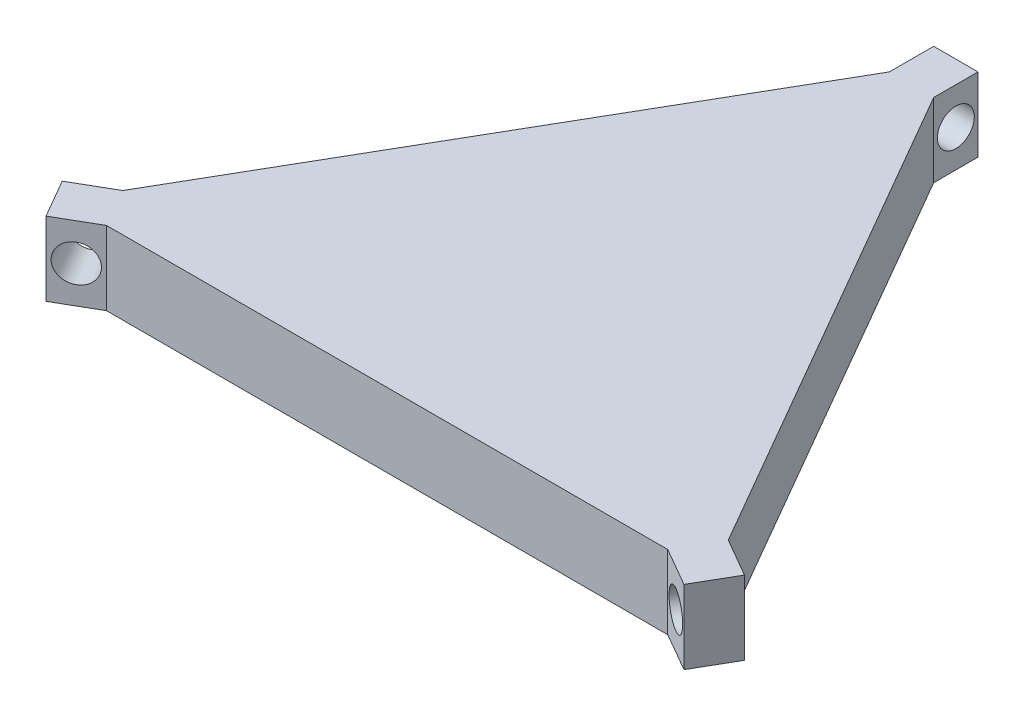
SolidWorks part; units mm, degrees
ref_plane "Front Plane" through (0, 0, 0) normal (0, 0, 1) x (1, 0, 0)
ref_plane "Top Plane" through (0, 0, 0) normal (0, 1, 0) x (1, 0, 0)
ref_plane "Right Plane" through (0, 0, 0) normal (1, 0, 0) x (0, 0, -1)
sketch "Sketch1" plane through (0, 0, 0) normal (0, 1, 0) x (1, 0, 0)
  line L6 (-3, 71.0141) -> (-41, 5.1962)
  line L7 (3, 71.0141) -> (41, 5.1962)
  line L8 (-38, 0) -> (38, 0)
  line L10 (-41, 5.1962) -> (-46.1962, 2.1962)
  line L11 (-38, 0) -> (-43.1962, -3)
  line L12 (-46.1962, 2.1962) -> (-43.1962, -3)
  line L14 (38, 0) -> (43.1962, -3)
  line L15 (41, 5.1962) -> (46.1962, 2.1962)
  line L16 (43.1962, -3) -> (46.1962, 2.1962)
  line L18 (3, 71.0141) -> (3, 77.0141)
  line L19 (-3, 71.0141) -> (-3, 77.0141)
  line L20 (3, 77.0141) -> (-3, 77.0141)
  point P1 (0, 0)
  dimension "D1" = 6
  dimension "D2" = 210
  dimension "D3" = 210
  dimension "D4" = 210
  dimension "D5" = 210
  dimension "D6" = 210
  dimension "D7" = 210
  dimension "D8" = 90
  dimension "D9" = 6
  dimension "D10" = 76
extrude "Boss-Extrude1" add sketch "Sketch1" along normal blind 10
sketch "Sketch2" plane through (-9.5, 0, -16.4545) normal (0.5, 0, 0.866) x (0.866, 0, -0.5)
  line L0 (-38.909, 10) -> (-32.909, 10) construction
  line L1 (-38.909, 10) -> (-38.909, 0) construction
  circle A0 centre (-35.909, 5) radius 2.5
  point P4 (-35.909, 10)
  point P7 (-38.909, 5)
  dimension "5" = 5
extrude "Cut-Extrude1" cut sketch "Sketch2" against normal up to surface (88.866 mm away)
ref_plane "Plane2" through (11, 0, -19.0526) normal (-0.5, 0, 0.866) x (0.866, 0, 0.5)
ref_plane "Plane3" through (0, 0, 0) normal (-1, 0, 0) x (0, 0, 1)
mirror "Mirror6" about plane through (0, 0, 0) normal (-1, 0, 0) of "Cut-Extrude1"
ref_plane "Plane4" through (-11, 0, -19.0526) normal (0.5, 0, 0.866) x (0.866, 0, -0.5)
sketch "Sketch3" plane through (-3, 0, 0) normal (-1, 0, 0) x (0, 0, 1)
  line L0 (-77.0141, 10) -> (-77.0141, 0) construction
  line L1 (-77.0141, 0) -> (-71.0141, 0) construction
  circle A0 centre (-74.0141, 5) radius 2.5
  dimension "D3" = 5
  dimension "D1" = 3
  dimension "D2" = 5
extrude "Cut-Extrude2" cut sketch "Sketch3" against normal up to surface (6 mm away) up to face at (3, 5, -74.0141)
